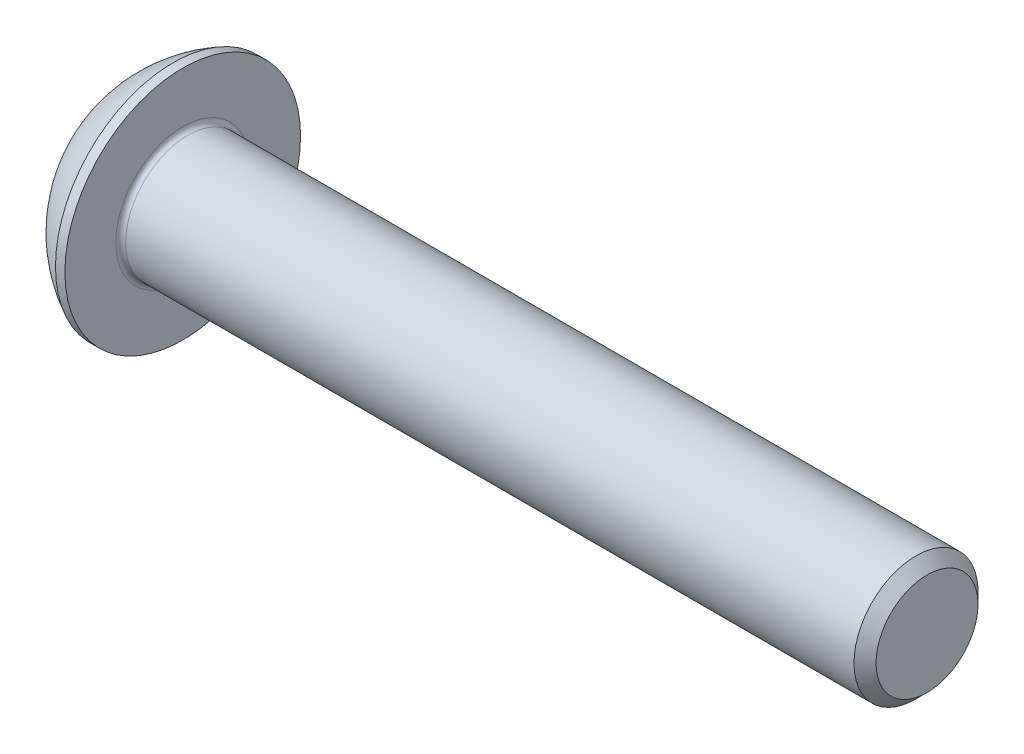
SolidWorks part; units mm, degrees
ref_plane "Plane1" through (0, 0, 0) normal (0, 0, 1) x (1, 0, 0)
ref_plane "Plane2" through (0, 0, 0) normal (0, 1, 0) x (1, 0, 0)
ref_plane "Plane3" through (0, 0, 0) normal (1, 0, 0) x (0, 0, -1)
revolve "BaseBody" add sketch "BodySke" angle 360 about L4
sketch "BodySke" plane through (0, 0, 0) normal (0, 0, 1) x (1, 0, 0)
  line L0 (32.75, 0) -> (32.75, 2.055)
  line L1 (32.305, 2.5) -> (2.75, 2.5)
  line L2 (2.75, 2.5) -> (2.75, 4.75)
  line L3 (2.75, 4.75) -> (2.37, 4.75)
  line L4 (0, 0) -> (101.6, 0) construction
  line L5 (2.75, -4.75) -> (2.37, -4.75) construction
  line L6 (55.6768, -2.5) -> (2.75, -2.5) construction
  line L7 (32.75, 0) -> (0, 0)
  line L8 (0, 2.375) -> (0, -2.375) construction
  line L9 (0, 0) -> (0, 2.375)
  line L10 (32.75, 2.055) -> (32.305, 2.5)
  line L11 (32.75, -2.055) -> (32.305, -2.5) construction
  line L12 (3.55, 9.525) -> (3.55, -2.5) construction
  line L13 (2.75, 9.525) -> (2.75, -2.5) construction
  arc A1 (0, 2.375) -> (2.37, 4.75) centre (4.755, 0) cw
  dimension "D1" = 4.75
  dimension "Diameter" = 5
  dimension "Length" = 30
  dimension "Head_dia" = 9.5
  dimension "Head_ht" = 2.75
  dimension "Head_side_ht" = 0.38
  dimension "Minor_dia" = 4.11
  dimension "Body_ch_ang" = 45
  dimension "Advance" = 0.8
  dimension "Thread_nom" = 30
cosmetic thread "ThreadCosmetic" [suppressed] parameters "Thread_length"=28.4, "Thread_minor"=4.11
fillet "Fillet1" radius 0.2 1 edges at (2.75, 0, 2.5)
sketch "Sketch2" plane through (0, 0, 0) normal (0, 0, 1) x (1, 0, 0)
  line L0 (0, 1.5) -> (1.56, 1.5)
  line L1 (1.56, 1.5) -> (2.426, 0)
  line L3 (2.426, 0) -> (0, 0)
  line L4 (0, 0) -> (0, 1.5)
  line L5 (0, -1.5) -> (1.56, -1.5) construction
  line L6 (0, 0) -> (47.625, 0) construction
  dimension "D2" = 60
  dimension "PreBroach_depth" = 1.56
  dimension "PreBroach_dia" = 3
revolve "PreBroach" cut sketch "Sketch2" angle 360 about L6
sketch "Sketch3" plane through (0, 0, 0) normal (1, 0, 0) x (0, 0, -1)
  line L0 (-1.5, -0.866) -> (-1.5, 0.866)
  line L1 (-1.5, 0.866) -> (0, 1.7321)
  line L2 (0, 1.7321) -> (1.5, 0.866)
  line L3 (1.5, 0.866) -> (1.5, -0.866)
  line L4 (1.5, -0.866) -> (0, -1.7321)
  line L5 (0, -1.7321) -> (-1.5, -0.866)
  dimension "D1" = 1.5
  dimension "D2" = 1.5
  dimension "D3" = 3
  dimension "Hex_size" = 3
extrude "Hex" cut sketch "Sketch3" along normal blind 1.56
sketch "ThdSchSke" plane through (0, 0, 0) normal (0, 0, 1) x (1, 0, 0)
  line L0 (4.35, -2.055) -> (4.0384, -2.5)
  line L1 (4.35, -2.055) -> (4.6616, -2.5)
  line L2 (4.6616, -2.5) -> (4.6616, -3.125)
  line L3 (-3.175, 0) -> (5.1513, 0) construction
  line L5 (4.6616, -3.125) -> (4.0384, -3.125)
  line L6 (4.0384, -3.125) -> (4.0384, -2.5)
  dimension "Thread_minor" = 4.11
  dimension "Diameter" = 5
  dimension "Start" = 4.35
  dimension "SideAngle" = 55
  dimension "VeeAngle" = 70
  dimension "Overcut" = 6.25
revolve "ThreadSchematic" [suppressed] cut sketch "ThdSchSke" angle 360 about L3
pattern_linear "ThdSchPat" [suppressed]
equation "\"D1@BodySke\" = \"Head_dia@BodySke\" * .5"
equation "\"Thread_minor@ThreadCosmetic\" = \"Minor_dia@BodySke\""
equation "\"D1@Sketch3\" = \"Hex_size@Sketch3\" / 2"
equation "\"D2@Sketch3\" = \"D1@Sketch3\""
equation "\"D3@Sketch3\" = \"Hex_size@Sketch3\""
equation "\"Thread_length@ThreadCosmetic\" = ((sgn( (\"Length@BodySke\" - \"Advance@BodySke\" * 2.0) - \"Thread_nom@BodySke\" )-1)*( (\"Length@BodySke\" - \"Advance@BodySke\" * 2.0) - \"Thread_nom@BodySke\" ))/-2+ \"Thread_nom@BodySke\""
equation "\"Thread_minor@ThdSchSke\" = \"Minor_dia@BodySke\""
equation "\"Diameter@ThdSchSke\" = \"Diameter@BodySke\""
equation "\"Overcut@ThdSchSke\" = \"Diameter@BodySke\" * 1.25"
equation "\"Start@ThdSchSke\" = \"Head_ht@BodySke\" + \"Length@BodySke\" - \"Thread_length@ThreadCosmetic\"  '---Non-countersunk---"
equation "\"Num_threads@ThdSchPat\" = int( \"Thread_length@ThreadCosmetic\" / \"Advance@BodySke\" + 0.999 )  + 1"
equation "\"Advance@ThdSchPat\" = \"Thread_length@ThreadCosmetic\" /  (\"Num_threads@ThdSchPat\" - 1) 'relax it"
equation "\"Num_threads@ThdSchPat\" = \"Num_threads@ThdSchPat\" - sgn( \"Num_threads@ThdSchPat\" - 1) '---chamfered tips only---"
